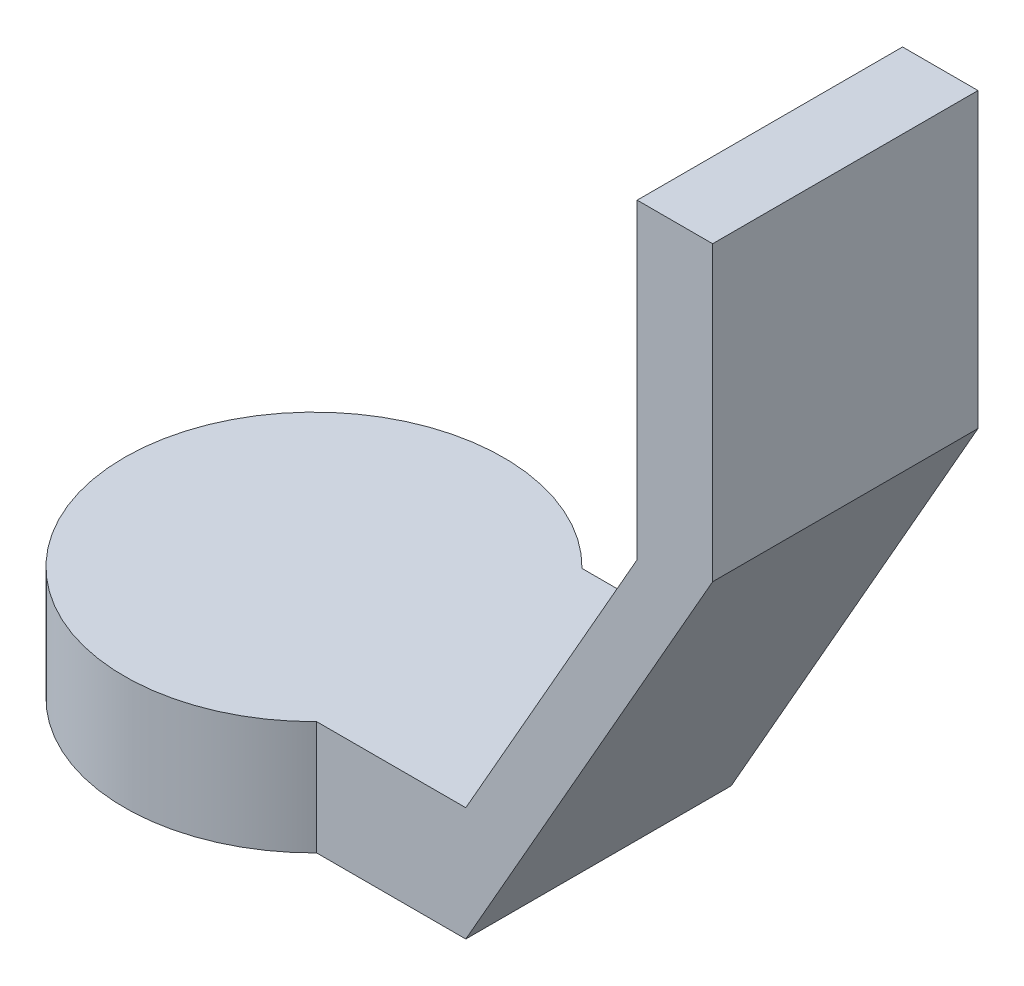
SolidWorks part; units mm, degrees
ref_plane "Front" through (0, 0, 0) normal (0, 0, 1) x (1, 0, 0)
ref_plane "Top" through (0, 0, 0) normal (0, 1, 0) x (1, 0, 0)
ref_plane "Right" through (0, 0, 0) normal (1, 0, 0) x (0, 0, -1)
sketch "草图1" plane through (0, 0, 0) normal (0, 1, 0) x (1, 0, 0)
  line L13 (0.0555, 35) -> (75.0555, 35)
  line L14 (0.0555, 35) -> (0.0555, -35)
  line L15 (0.0555, -35) -> (75.0555, -35)
  line L16 (75.0555, 35) -> (75.0555, -35)
  circle A1 centre (0, 0) radius 50
  dimension "D1" = 100
  dimension "D2" = 35
  dimension "D3" = 35
  dimension "D4" = 75
extrude "凸台-拉伸1" add sketch "草图1" along normal blind 30 contours A1 L15 L16 L13 | L15 A1 L13 L14 | L13 A1 L15 L14
sketch "草图2" plane through (0, 0, 35) normal (0, 0, 1) x (1, 0, 0)
  line L0 (75.0555, 0) -> (140.1741, 114.1921)
  line L1 (140.1741, 114.1921) -> (140.1741, 191.4116)
  line L2 (140.1741, 191.4116) -> (120.2689, 191.4116)
  line L3 (120.2689, 191.4116) -> (120.2689, 109.2863)
  line L5 (120.2689, 109.2863) -> (75.0555, 30)
  line L6 (75.0555, 30) -> (75.0555, 0)
extrude "凸台-拉伸2" add sketch "草图2" against normal blind 70 contours L2 L3 L5 L6 L0 L1
